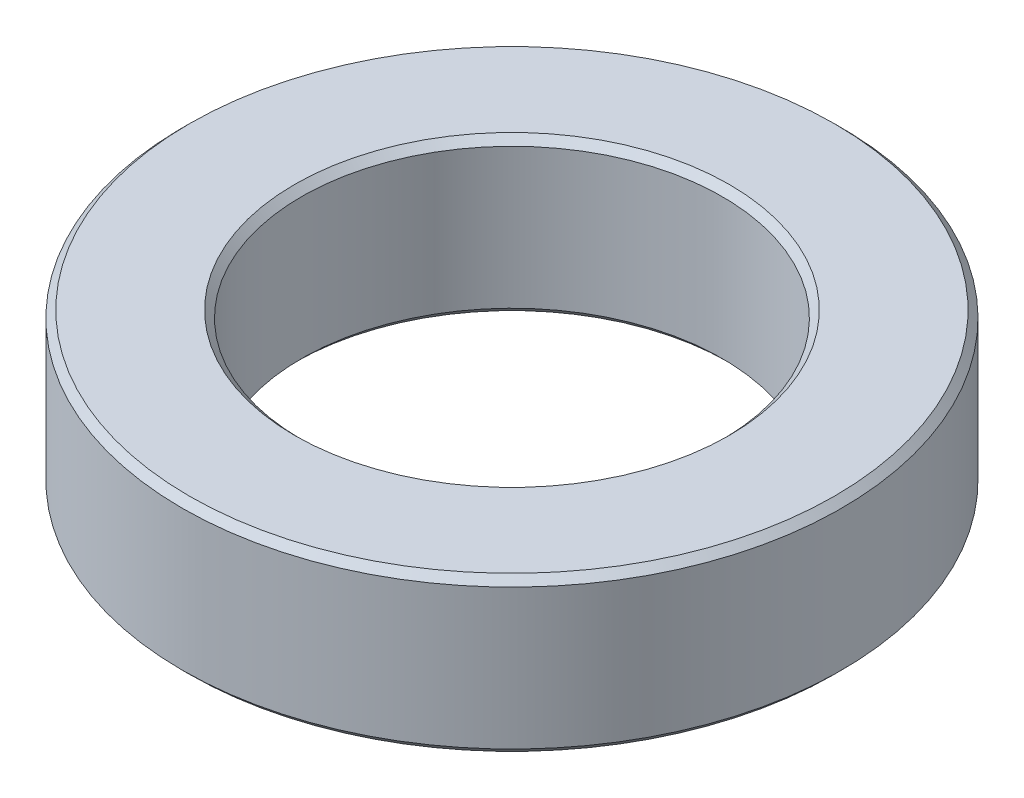
SolidWorks part; units mm, degrees
ref_plane "前视基准面" through (0, 0, 0) normal (0, 0, 1) x (1, 0, 0)
ref_plane "上视基准面" through (0, 0, 0) normal (0, 1, 0) x (1, 0, 0)
ref_plane "右视基准面" through (0, 0, 0) normal (1, 0, 0) x (0, 0, -1)
sketch "草图1" plane through (0, 0, 0) normal (0, 1, 0) x (1, 0, 0)
  circle A0 centre (0, 0) radius 15
  circle A1 centre (0, 0) radius 23.5
  dimension "D1" = 30
  dimension "D2" = 47
extrude "凸台-拉伸1" add sketch "草图1" along normal blind 11
chamfer "倒角1" distance 0.5 angle 45 4 edges at (0, 0, 23.5) (0, 0, 15) (0, 11, 15) (0, 11, 23.5)
